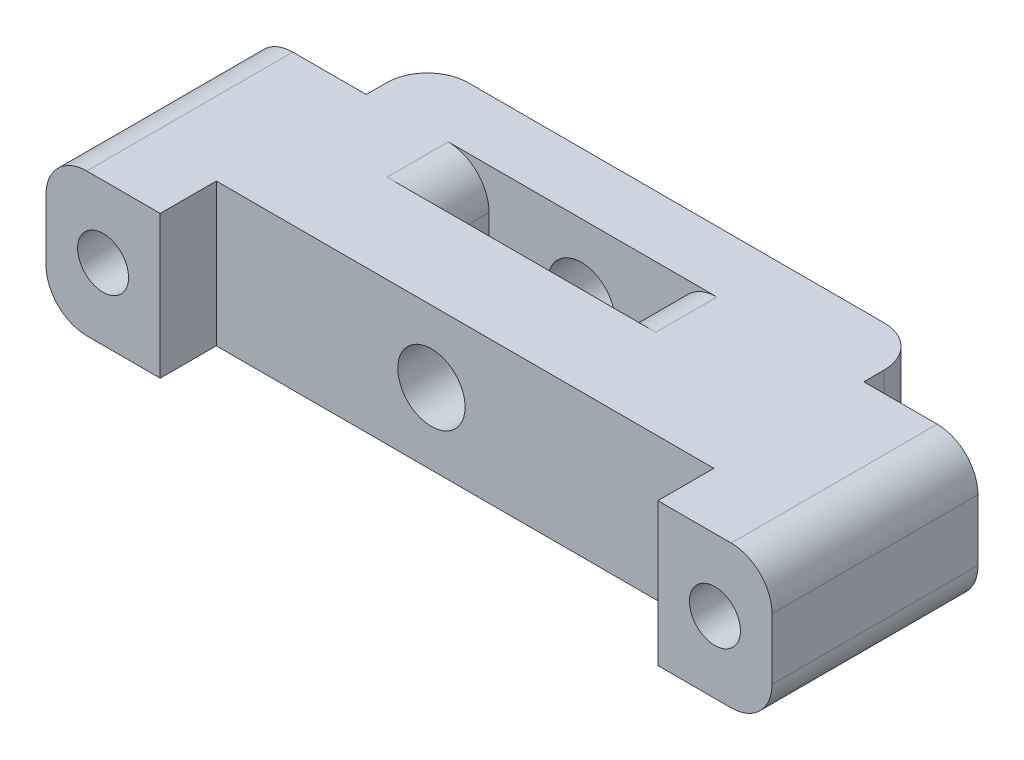
SolidWorks part; units mm, degrees
material "ABS"
ref_plane "Front Plane" through (0, 0, 0) normal (0, 0, 1) x (1, 0, 0)
ref_plane "Top Plane" through (0, 0, 0) normal (0, 1, 0) x (1, 0, 0)
ref_plane "Right Plane" through (0, 0, 0) normal (1, 0, 0) x (0, 0, -1)
sketch "Sketch1" plane through (0, 0, 0) normal (0, 1, 0) x (1, 0, 0)
  line L0 (0, 0) -> (0, 10.35) construction
  line L1 (-17.8, 10.35) -> (17.8, 10.35)
  line L2 (-17.8, 10.35) -> (-17.8, -2.75)
  line L3 (-17.8, -2.75) -> (-12.2, -2.75)
  line L4 (-12.2, -2.75) -> (-12.2, 0)
  line L5 (17.8, 10.35) -> (17.8, -2.75)
  line L6 (17.8, -2.75) -> (12.2, -2.75)
  line L7 (12.2, -2.75) -> (12.2, 0)
  line L8 (12.2, 0) -> (-12.2, 0)
  line L9 (0, 5.85) -> (17.8, 5.85) construction
  line L11 (-6.175, 7.35) -> (3, 7.35)
  line L12 (-6.175, 7.35) -> (-6.175, 4.35)
  line L13 (-6.175, 4.35) -> (3, 4.35)
  line L14 (3, 7.35) -> (3, 4.35)
  point P10 (0, 2.85)
  point P12 (0, 5.85)
  dimension "D1" = 5.6
  dimension "D2" = 24.4
  dimension "D3" = 2.75
  dimension "D4" = 2.85
  dimension "D5" = 3
  dimension "D6" = 6.175
  dimension "D7" = 3
  dimension "D8" = 3
  dimension "D9" = 3
extrude "Boss-Extrude1" add sketch "Sketch1" along normal mid plane 7
sketch "Sketch2" plane through (0, 0, -10.35) normal (0, 0, -1) x (-1, 0, 0)
  line L0 (0, -3.5) -> (0, 3.5) construction
  line L1 (-17.8, -3.5) -> (17.8, -3.5) construction
  line L2 (-17.8, 3.5) -> (17.8, 3.5) construction
  line L3 (17.8, 0) -> (-17.8, 0) construction
  line L4 (17.8, 3.5) -> (17.8, -3.5) construction
  line L5 (-17.8, 3.5) -> (-17.8, -3.5) construction
  circle A0 centre (15, 0) radius 1.25
  circle A1 centre (1.65, 0) radius 1.65
  circle A2 centre (-15, 0) radius 1.25
  dimension "D1" = 3.3
  dimension "D2" = 2.5
  dimension "D3" = 15
extrude "Cut-Extrude1" cut sketch "Sketch2" against normal through all
sketch "Sketch3" plane through (0, 0, -10.35) normal (0, 0, -1) x (-1, 0, 0)
  line L0 (-17.8, 3.5) -> (17.8, 3.5) construction
  line L1 (17.8, -3.5) -> (12.2, -3.5)
  line L2 (17.8, -3.5) -> (17.8, 3.5)
  line L3 (17.8, 3.5) -> (12.2, 3.5)
  line L4 (12.2, -3.5) -> (12.2, 3.5)
  line L5 (0, -3.5) -> (0, 3.5) construction
  line L6 (-17.8, -3.5) -> (17.8, -3.5) construction
  line L7 (17.8, 3.5) -> (12.2, 3.5) construction
  line L8 (-12.2, -3.5) -> (-12.2, 3.5)
  line L9 (-17.8, 3.5) -> (-12.2, 3.5)
  line L10 (-17.8, -3.5) -> (-17.8, 3.5)
  line L11 (-17.8, -3.5) -> (-12.2, -3.5)
extrude "Cut-Extrude2" cut sketch "Sketch3" against normal blind 3
fillet "Fillet1" radius 2 10 edges at (12.2, 0, -10.35) (-12.2, 0, -10.35) (17.8, 3.5, -2.3) (17.8, -3.5, -2.3) (-17.8, 3.5, -2.3) (-17.8, -3.5, -2.3) (3, -3.5, -5.85) (-6.175, -3.5, -5.85) (3, 3.5, -5.85) (-6.175, 3.5, -5.85)
equation "\"D6@Sketch1\"=\"pin diameter@values@params_print.sldprt\"+\"width keep@values@params_print.sldprt\""
equation "\"D7@Sketch1\"=\"width keep@values@params_print.sldprt\""
equation "\"D8@Sketch1\"=\"D7@Sketch1\""
equation "\"D9@Sketch1\"=\"D7@Sketch1\""
equation "\"D1@Sketch2\"=\"pin diameter@values@params_print.sldprt\"+\"print fit@values@params_print.sldprt\""
